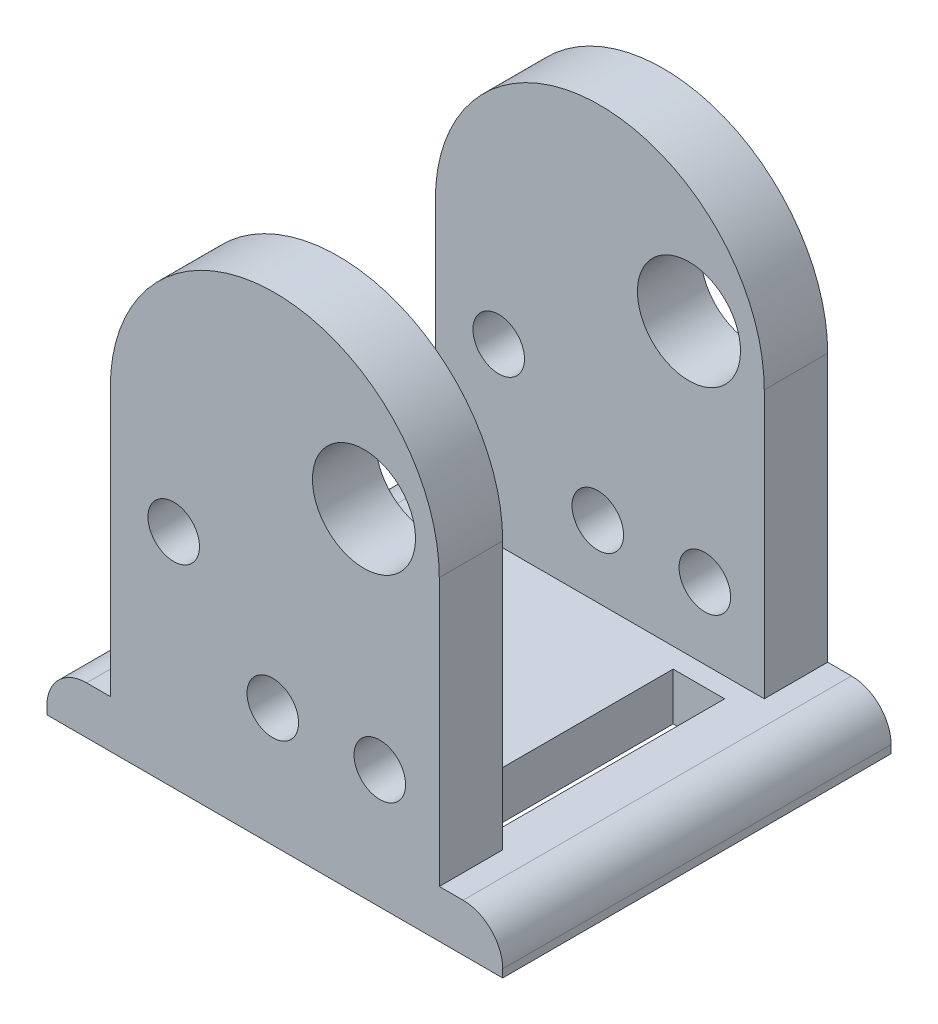
SolidWorks part; units mm, degrees
ref_plane "Front Plane" through (0, 0, 0) normal (0, 0, 1) x (1, 0, 0)
ref_plane "Top Plane" through (0, 0, 0) normal (0, 1, 0) x (1, 0, 0)
ref_plane "Right Plane" through (0, 0, 0) normal (1, 0, 0) x (0, 0, -1)
sketch "Sketch1" plane through (0, 0, 0) normal (0, 0, 1) x (1, 0, 0)
  line L0 (-14.605, 0) -> (14.605, 0)
  line L1 (0, -5.9457) -> (0, 16.8537) construction
  line L2 (-14.605, 0) -> (-14.605, 3.048)
  line L3 (-14.605, 3.048) -> (-10.541, 3.048)
  line L4 (-10.541, 3.048) -> (-10.541, 20.193)
  line L5 (10.541, 20.193) -> (10.541, 3.048)
  line L6 (10.541, 3.048) -> (14.605, 3.048)
  line L7 (14.605, 3.048) -> (14.605, 0)
  arc A0 (-10.541, 20.193) -> (10.541, 20.193) centre (0, 20.193) cw
  dimension "D2" = 30.734
  dimension "D1" = 29.21
  dimension "D3" = 21.082
  dimension "D4" = 3.048
extrude "Boss-Extrude1" add sketch "Sketch1" along normal blind 24.892
sketch "Sketch2" plane through (-10.541, 0, 0) normal (-1, 0, 0) x (0, 0, 1)
  line L0 (12.446, 20.193) -> (12.446, 6.9771) construction
  line L3 (4.064, 3.048) -> (4.064, 30.734)
  line L4 (24.892, 3.048) -> (0, 3.048) construction
  line L5 (24.892, 30.734) -> (0, 30.734) construction
  line L6 (4.064, 30.734) -> (20.828, 30.734)
  line L7 (20.828, 30.734) -> (20.828, 3.048)
  line L8 (24.892, 3.048) -> (0, 3.048) construction
  line L9 (20.828, 3.048) -> (4.064, 3.048)
  dimension "D1" = 12.446
  dimension "D2" = 16.764
extrude "Cut-Extrude1" cut sketch "Sketch2" against normal up to next
sketch "Sketch3" plane through (0, 0, 0) normal (0, 0, -1) x (-1, 0, 0)
  line L0 (-5.715, 21.59) -> (-14.605, 0) construction
  line L1 (-14.605, 0) -> (-6.731, 7.62) construction
  line L2 (-14.605, 0) -> (0.127, 7.62) construction
  line L3 (-14.605, 0) -> (6.477, 14.224) construction
  circle A0 centre (-5.715, 21.59) radius 3.302
  circle A1 centre (-6.731, 7.62) radius 1.651
  circle A2 centre (0.127, 7.62) radius 1.651
  circle A3 centre (6.477, 14.224) radius 1.651
  dimension "D9" = 6.604
  dimension "D10" = 3.302
  dimension "D11" = 3.302
  dimension "D12" = 3.302
  dimension "D1" = 7.62
  dimension "D2" = 7.874
  dimension "D3" = 7.62
  dimension "D4" = 14.732
  dimension "D5" = 14.224
  dimension "D6" = 21.082
  dimension "D7" = 21.59
  dimension "D8" = 8.89
extrude "Cut-Extrude2" cut sketch "Sketch3" against normal up to surface (24.892 mm away) up to face at (0, 7.8899, 24.892)
sketch "Sketch4" plane through (0, 0, 0) normal (0, -1, 0) x (1, 0, 0)
  line L0 (0, 0) -> (0, 24.892) construction
  line L1 (-9.2268, 19.558) -> (-5.4168, 19.558)
  line L2 (-9.2268, 19.558) -> (-9.2268, 5.334)
  line L3 (-9.2268, 5.334) -> (-5.4168, 5.334)
  line L4 (-5.4168, 19.558) -> (-5.4168, 5.334)
  line L5 (5.969, 19.558) -> (9.271, 19.558)
  line L6 (5.969, 19.558) -> (5.969, 5.334)
  line L7 (5.969, 5.334) -> (9.271, 5.334)
  line L8 (9.271, 19.558) -> (9.271, 5.334)
  line L9 (-14.605, 0) -> (14.605, 0) construction
  line L10 (-14.605, 24.892) -> (14.605, 24.892) construction
  line L11 (-14.605, 12.446) -> (14.605, 12.446) construction
  line L12 (-14.605, 24.892) -> (-14.605, 0) construction
  line L13 (14.605, 24.892) -> (14.605, 0) construction
  dimension "D1" = 3.81
  dimension "D2" = 3.302
  dimension "D3" = 5.3782
  dimension "D4" = 14.224
  dimension "D5" = 20.574
extrude "Cut-Extrude3" cut sketch "Sketch4" against normal up to next
fillet "Fillet1" radius 2.54 2 edges at (-14.605, 3.048, 12.446) (14.605, 3.048, 12.446)
